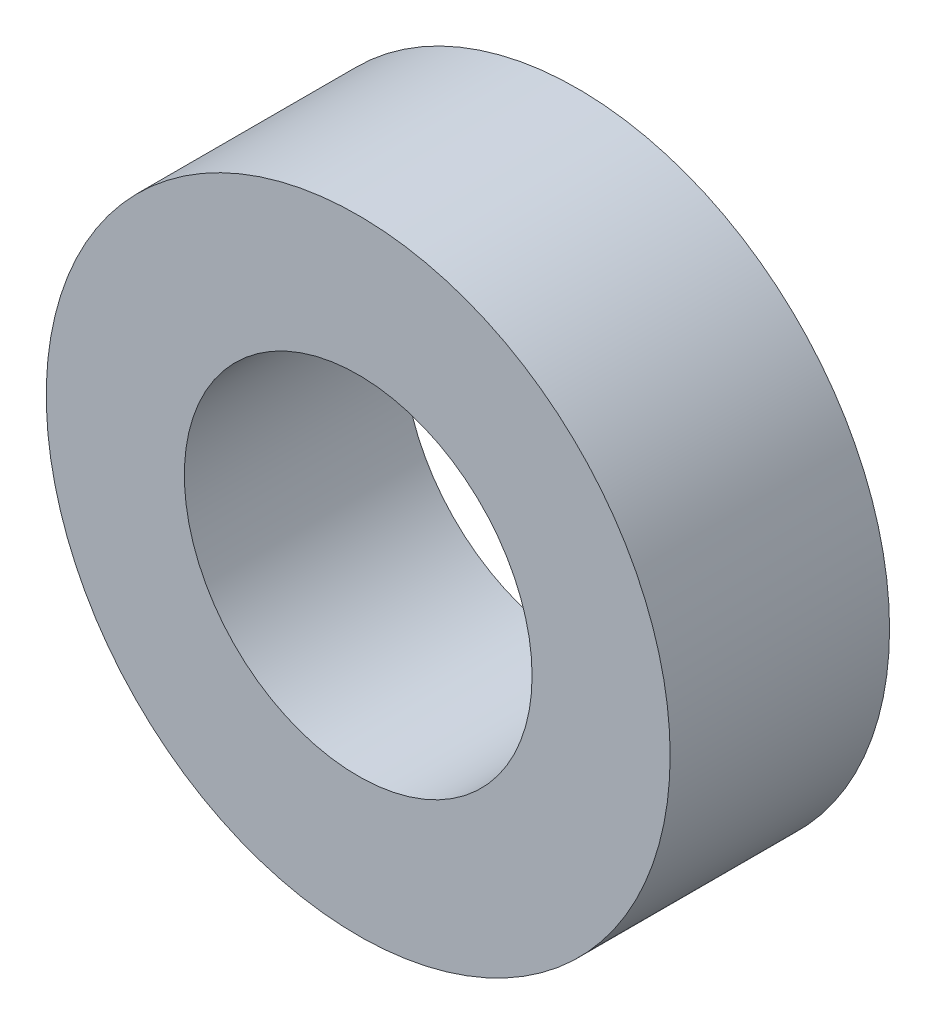
SolidWorks part; units mm, degrees
material "ABS"
ref_plane "Front Plane" through (0, 0, 0) normal (0, 0, 1) x (1, 0, 0)
ref_plane "Top Plane" through (0, 0, 0) normal (0, 1, 0) x (1, 0, 0)
ref_plane "Right Plane" through (0, 0, 0) normal (1, 0, 0) x (0, 0, -1)
sketch "Sketch1" plane through (0, 0, 0) normal (0, 0, 1) x (1, 0, 0)
  circle A0 centre (0, 0) radius 40.259
  circle A1 centre (0, 0) radius 72.2313
  dimension "D1" = 144.4625
  dimension "D2" = 80.518
extrude "Boss-Extrude1" add sketch "Sketch1" along normal blind 50.8
